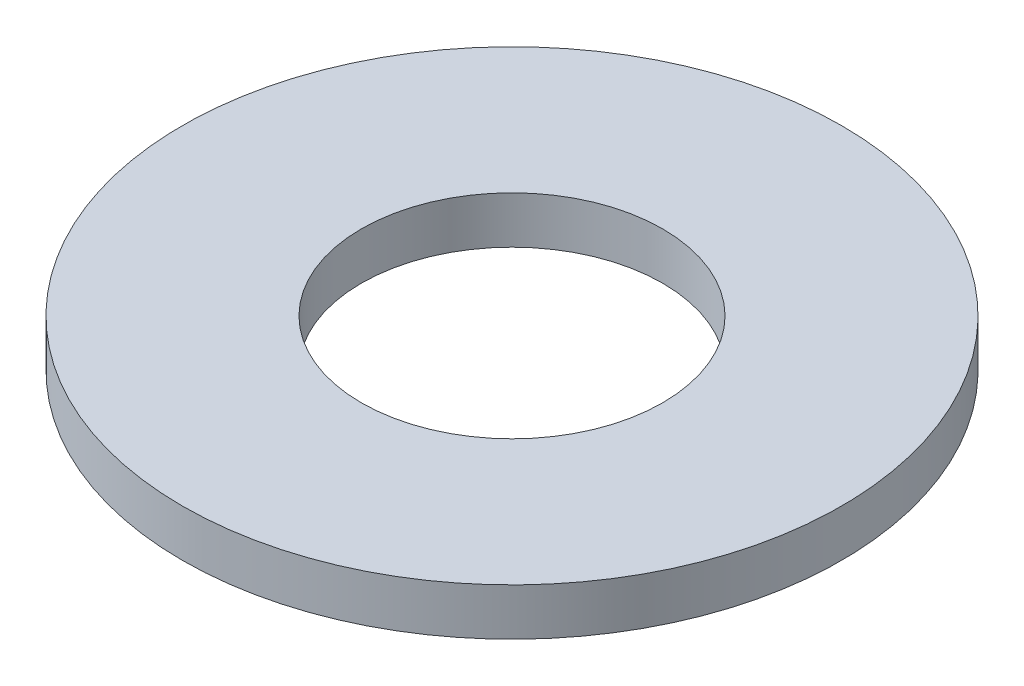
SolidWorks part; units mm, degrees
material "Acier allié"
ref_plane "Plan de face" through (0, 0, 0) normal (0, 0, 1) x (1, 0, 0)
ref_plane "Plan de dessus" through (0, 0, 0) normal (0, 1, 0) x (1, 0, 0)
ref_plane "Plan de droite" through (0, 0, 0) normal (1, 0, 0) x (0, 0, -1)
sketch "Esquisse1" plane through (0, 0, 0) normal (0, 1, 0) x (1, 0, 0)
  circle A0 centre (0, 0) radius 3.5
  circle A1 centre (0, 0) radius 1.6
  dimension "D1" = 7
  dimension "D2" = 3.2
extrude "Boss.-Extru.1" add sketch "Esquisse1" along normal blind 0.5
